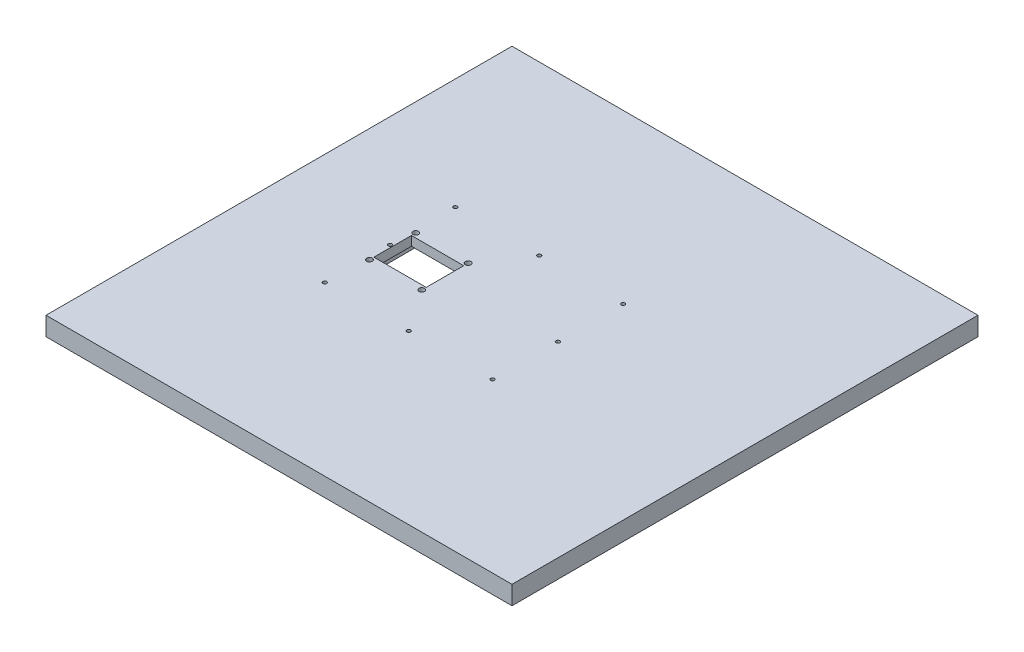
SolidWorks part; units mm, degrees
ref_plane "Front Plane" through (0, 0, 0) normal (0, 0, 1) x (1, 0, 0)
ref_plane "Top Plane" through (0, 0, 0) normal (0, 1, 0) x (1, 0, 0)
ref_plane "Right Plane" through (0, 0, 0) normal (1, 0, 0) x (0, 0, -1)
sketch "Sketch1" plane through (0, 0, 0) normal (0, 1, 0) x (1, 0, 0)
  line L0 (-250, 0) -> (250, 0) construction
  line L1 (-250, 250) -> (250, 250)
  line L2 (-250, 250) -> (-250, -250)
  line L3 (-250, -250) -> (250, -250)
  line L4 (250, 250) -> (250, -250)
  line L5 (-250, 250) -> (250, -250) construction
  line L6 (-250, -250) -> (250, 250) construction
  line L12 (-121, 21) -> (-79, 21) construction
  line L13 (-121, 21) -> (-121, -21) construction
  line L18 (-121, -21) -> (-79, -21) construction
  line L19 (-79, 21) -> (-79, -21) construction
  line L20 (-121, 21) -> (-79, -21) construction
  line L21 (-121, -21) -> (-79, 21) construction
  line L26 (-135, 31) -> (-65, 31) construction
  line L27 (-135, 31) -> (-135, -31) construction
  line L28 (-135, -31) -> (-65, -31) construction
  line L29 (-65, 31) -> (-65, -31) construction
  line L30 (-135, 31) -> (-65, -31) construction
  line L31 (-135, -31) -> (-65, 31) construction
  circle A4 centre (-100, 0) radius 23 construction
  circle A5 centre (-116.2548, 16.2548) radius 2.25 construction
  circle A6 centre (-83.7365, 16.2635) radius 2.25 construction
  circle A7 centre (-100, 0) radius 37.5 construction
  circle A8 centre (-128.0721, 24.8638) radius 3
  circle A9 centre (-71.9279, 24.8638) radius 3
  circle A10 centre (-71.9279, -24.8638) radius 3
  circle A11 centre (-128.0721, -24.8638) radius 3
  point P0 (0, 0)
  point P10 (-100, 0)
  point P13 (-100, 0)
  point P20 (-131.2548, 16.2548)
  dimension "D7" = 70
  dimension "D6" = 15
  dimension "D9" = 75
  dimension "D1" = 500
  dimension "D2" = 500
  dimension "D3" = 150
  dimension "D4" = 42
  dimension "D5" = 42
  dimension "D8" = 62
extrude "Boss-Extrude1" add sketch "Sketch1" along normal blind 20
sketch "Sketch2" plane through (0, 20, 0) normal (0, 1, 0) x (1, 0, 0)
  line L0 (-250, 0) -> (250, 0) construction
  line L1 (-250, 250) -> (-250, -250) construction
  line L2 (250, -250) -> (250, 250) construction
  line L9 (-128.0721, 20.1443) -> (-128.0721, -20.1443)
  line L11 (-71.9279, 20.1443) -> (-71.9279, -20.1443)
  line L15 (-128.0721, 20.1443) -> (-71.9279, 20.1443)
  line L16 (-128.0721, -20.1443) -> (-71.9279, -20.1443)
  line L19 (240, -240) -> (240, 240)
  line L20 (240, 240) -> (-240, 240)
  line L21 (-240, 240) -> (-240, -240)
  line L22 (-240, -240) -> (240, -240)
  line L23 (240, -240) -> (240, 240)
  line L24 (240, 240) -> (-240, 240)
  line L25 (-240, 240) -> (-240, -240)
  line L26 (-240, -240) -> (240, -240)
  dimension "D1" = 10
extrude "Cut-Extrude2" cut sketch "Sketch2" against normal through all contours L9 L0 L11 L15 | L0 L9 L16 L11
sketch "Sketch3" plane through (0, 0, 0) normal (0, -1, 0) x (1, 0, 0)
  line L0 (-128.0721, 24.8638) -> (-71.9279, -24.8638) construction
  line L2 (-65.3951, -33.7796) -> (-134.6049, -33.7796)
  line L3 (-65.3951, -33.7796) -> (-65.3951, 33.7796)
  line L4 (-65.3951, 33.7796) -> (-134.6049, 33.7796)
  line L5 (-134.6049, -33.7796) -> (-134.6049, 33.7796)
  line L6 (-65.3951, -33.7796) -> (-134.6049, 33.7796) construction
  line L7 (-65.3951, 33.7796) -> (-134.6049, -33.7796) construction
  point P4 (-100, 0)
extrude "Cut-Extrude3" cut sketch "Sketch3" against normal blind 10
sketch "Sketch4" plane through (0, 20, 0) normal (0, 1, 0) x (1, 0, 0)
  line L0 (-250, 0) -> (250, 0) construction
  line L1 (-250, 250) -> (-250, -250) construction
  line L2 (250, -250) -> (250, 250) construction
  line L3 (-40.8146, 0) -> (-40.8146, 75) construction
  line L4 (-140.8146, 75) -> (59.1854, 75) construction
  line L5 (-140.8146, 75) -> (-140.8146, -75) construction
  line L6 (-140.8146, -75) -> (59.1854, -75) construction
  line L7 (59.1854, 75) -> (59.1854, -75) construction
  line L8 (-140.8146, 75) -> (59.1854, -75) construction
  line L9 (-140.8146, -75) -> (59.1854, 75) construction
  line L10 (-130.8146, 70) -> (49.1854, 70) construction
  line L11 (49.1854, 70) -> (49.1854, -70) construction
  circle A0 centre (-130.8146, 70) radius 2
  circle A1 centre (49.1854, 70) radius 2
  circle A2 centre (-40.8146, 70) radius 2
  circle A3 centre (-130.8146, -70) radius 2
  circle A4 centre (-40.8146, -70) radius 2
  circle A5 centre (49.1854, -70) radius 2
  circle A6 centre (49.1854, 0) radius 2
  circle A7 centre (-130.8146, 0) radius 2
  point P6 (-40.8146, 0)
  point P11 (-130.8146, 70)
  dimension "D1" = 200
  dimension "D2" = 150
  dimension "D3" = 10
  dimension "D4" = 5
extrude "Cut-Extrude4" cut sketch "Sketch4" against normal through all
